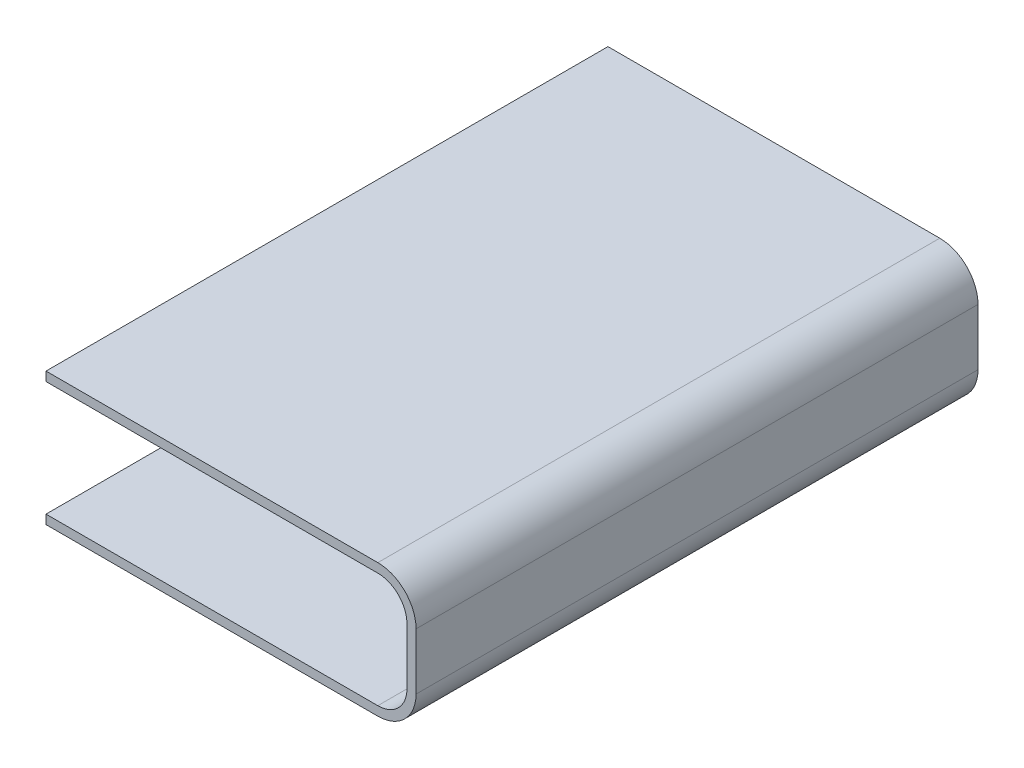
SolidWorks part; units mm, degrees
ref_plane "Front Plane" through (0, 0, 0) normal (0, 0, 1) x (1, 0, 0)
ref_plane "Top Plane" through (0, 0, 0) normal (0, 1, 0) x (1, 0, 0)
ref_plane "Right Plane" through (0, 0, 0) normal (1, 0, 0) x (0, 0, -1)
sketch "Sketch1" plane through (0, 0, 0) normal (0, 0, 1) x (1, 0, 0)
  line L0 (0, 0.3969) -> (0, -0.3969)
  line L1 (-152.4, 0) -> (152.4, 0) construction
  point P6 (0, 0)
  dimension "Width" = 304.8
  dimension "Thickness" = 0.7937
sketch "Sketch2" plane through (0, 0, 0) normal (1, 0, 0) x (0, 0, -1)
  line L0 (152.4, 0) -> (-152.4, 0)
  point P4 (0, 0)
  dimension "Length" = 304.8
sketch "Sketch3" plane through (0, 0, 0) normal (0, 0, 1) x (1, 0, 0)
  line L1 (152.4, 0.3969) -> (-152.4, 0.3969)
  line L2 (152.4, 0.3969) -> (152.4, -0.3969)
  line L3 (152.4, -0.3969) -> (-152.4, -0.3969)
  line L4 (-152.4, 0.3969) -> (-152.4, -0.3969)
  line L5 (152.4, 0.3969) -> (-152.4, -0.3969) construction
  line L6 (152.4, -0.3969) -> (-152.4, 0.3969) construction
  point P0 (0, 0)
extrude "Boss-Extrude1" add sketch "Sketch3" along normal up to vertex (152.4 mm away) and the other way up to vertex (152.4 mm away) up to point (0, 0, 152.4) other way up to point (0, 0, -152.4)
sketch "Sketch4" plane through (0, 0, 0) normal (0, 1, 0) x (1, 0, 0)
  line L1 (-152.4, -152.4) -> (-123.4694, -152.4)
  line L2 (-152.4, -152.4) -> (-152.4, -103.4034)
  line L3 (-152.4, -103.4034) -> (-123.4694, -103.4034)
  line L4 (-123.4694, -152.4) -> (-123.4694, -103.4034)
  dimension "D1" = 28.9306
  dimension "D2" = 48.9966
extrude "Cut-Extrude1" cut sketch "Sketch4" along normal through all both and the other way through all flip side to cut
ref_plane "Plane1" through (-137.9347, 0, 0) normal (-1, 0, 0) x (0, 0, 1)
ref_plane "Plane2" through (0, 0, 127.9017) normal (0, 0, 1) x (1, 0, 0)
sketch "Sketch5" plane through (0, 0, 127.9017) normal (0, 0, 1) x (1, 0, 0)
  line L0 (-152.4, -10.4045) -> (-123.4694, -10.4045)
  line L1 (-152.4, 0.3969) -> (-152.4, -0.3969) construction
  line L2 (-120.9294, -7.8645) -> (-120.9294, -2.9369)
  line L3 (-123.4694, -0.3969) -> (-152.4, -0.3969)
  line L4 (-152.4, -0.3969) -> (-123.4694, -0.3969) construction
  line L5 (-123.4694, 0.3969) -> (-123.4694, -0.3969) construction
  arc A0 (-123.4694, -10.4045) -> (-120.9294, -7.8645) centre (-123.4694, -7.8645) ccw
  arc A1 (-120.9294, -2.9369) -> (-123.4694, -0.3969) centre (-123.4694, -2.9369) ccw
  point P2 (-123.1328, 6.9003)
  point P14 (-123.4071, -0.3969)
  point P15 (-118.2184, -2.9369)
  point P16 (0, 0)
  point P19 (-152.4, -0.3969)
  point P20 (-150.448, -0.3969)
  dimension "D1" = 2.54
  dimension "D2" = 10.0076
extrude "Extrude-Thin1" add sketch "Sketch5" against normal up to surface and the other way up to surface thin
